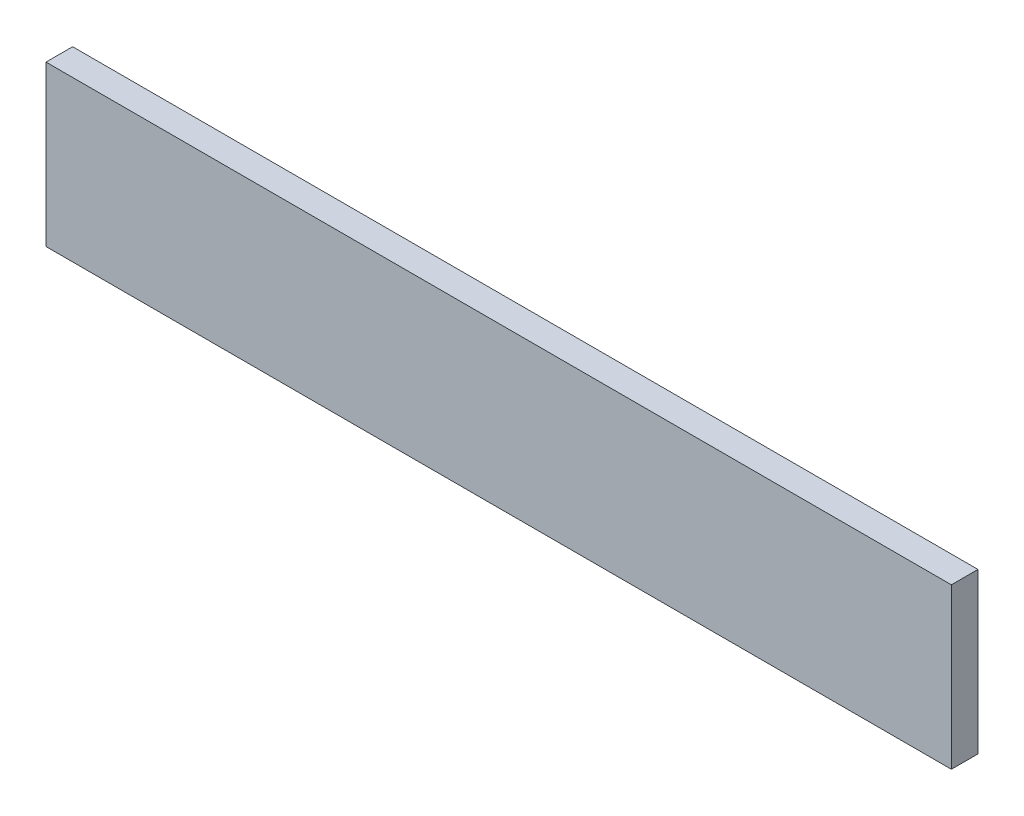
SolidWorks part; units mm, degrees
ref_plane "Front Plane" through (0, 0, 0) normal (0, 0, 1) x (1, 0, 0)
ref_plane "Top Plane" through (0, 0, 0) normal (0, 1, 0) x (1, 0, 0)
ref_plane "Right Plane" through (0, 0, 0) normal (1, 0, 0) x (0, 0, -1)
sketch "Sketch1" plane through (0, 0, 0) normal (0, 0, 1) x (1, 0, 0)
  line L1 (0, 0) -> (215.9, 0)
  line L2 (0, 0) -> (0, 38.1)
  line L3 (0, 38.1) -> (215.9, 38.1)
  line L4 (215.9, 0) -> (215.9, 38.1)
  dimension "D1" = 38.1
  dimension "D2" = 215.9
extrude "Boss-Extrude1" add sketch "Sketch1" along normal blind 6.35
